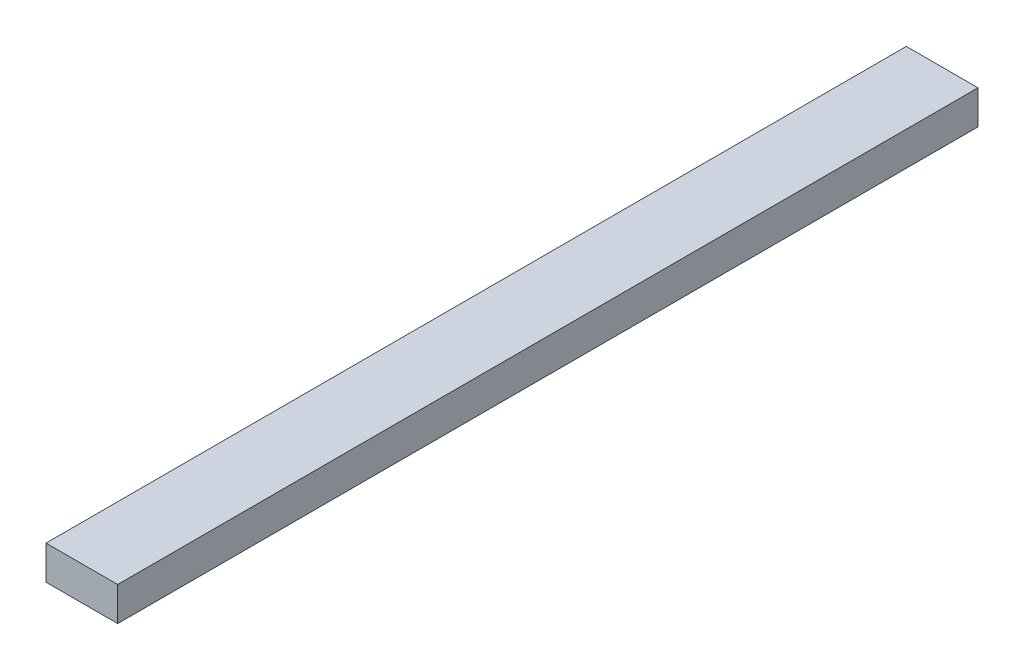
SolidWorks part; units mm, degrees
ref_plane "Front" through (0, 0, 0) normal (0, 0, 1) x (1, 0, 0)
ref_plane "Top" through (0, 0, 0) normal (0, 1, 0) x (1, 0, 0)
ref_plane "Right" through (0, 0, 0) normal (1, 0, 0) x (0, 0, -1)
sketch "Sketch1" plane through (0, 0, 0) normal (0, 0, 1) x (1, 0, 0)
  line L1 (3.175, -1.5) -> (-3.175, -1.5)
  line L2 (3.175, -1.5) -> (3.175, 1.5)
  line L3 (3.175, 1.5) -> (-3.175, 1.5)
  line L4 (-3.175, -1.5) -> (-3.175, 1.5)
  line L5 (3.175, -1.5) -> (-3.175, 1.5) construction
  line L6 (3.175, 1.5) -> (-3.175, -1.5) construction
  point P0 (0, 0)
  dimension "D1" = 6.35
  dimension "D2" = 3
extrude "Boss-Extrude1" add sketch "Sketch1" along normal blind 76.2
